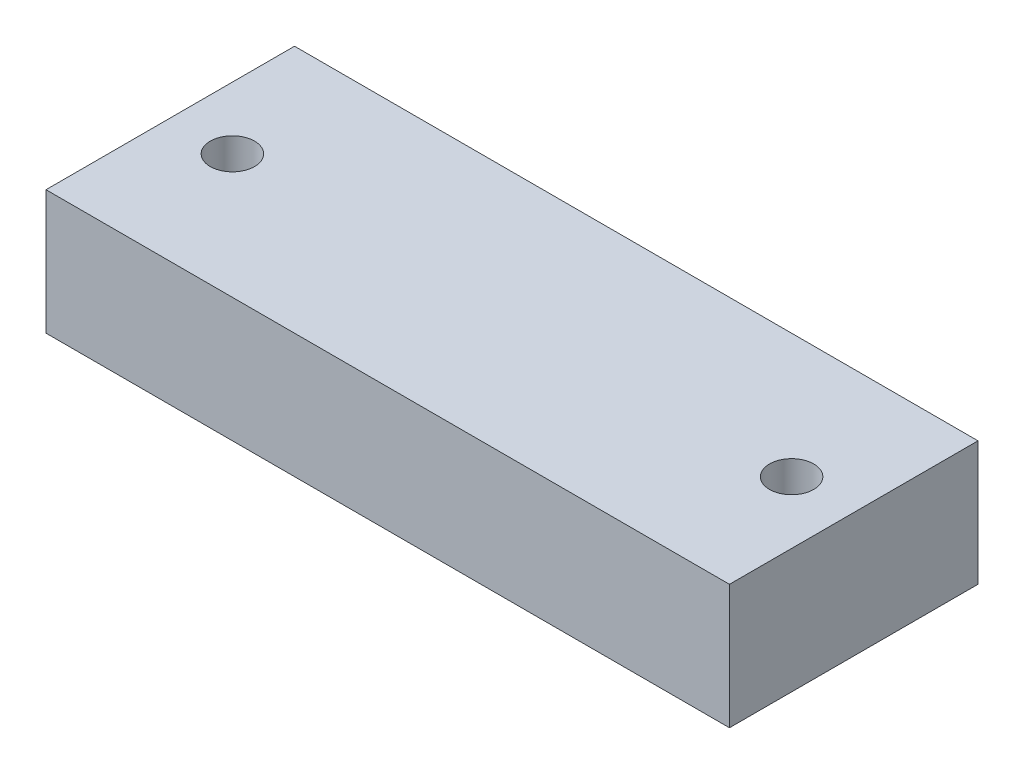
SolidWorks part; units mm, degrees
ref_plane "Front Plane" through (0, 0, 0) normal (0, 0, 1) x (1, 0, 0)
ref_plane "Top Plane" through (0, 0, 0) normal (0, 1, 0) x (1, 0, 0)
ref_plane "Right Plane" through (0, 0, 0) normal (1, 0, 0) x (0, 0, -1)
sketch "Sketch1" plane through (0, 0, 0) normal (0, 1, 0) x (1, 0, 0)
  line L1 (-17.4625, 6.35) -> (17.4625, 6.35)
  line L2 (-17.4625, 6.35) -> (-17.4625, -6.35)
  line L3 (-17.4625, -6.35) -> (17.4625, -6.35)
  line L4 (17.4625, 6.35) -> (17.4625, -6.35)
  line L5 (-17.4625, 6.35) -> (17.4625, -6.35) construction
  line L6 (-17.4625, -6.35) -> (17.4625, 6.35) construction
  point P0 (0, 0)
  dimension "D1" = 34.925
  dimension "D2" = 12.7
extrude "Boss-Extrude1" add sketch "Sketch1" along normal blind 6.35
hole_wizard "#4-40 Tapped Hole1" positions "Sketch2" profile "Sketch3" tap size "#4-40" standard "ANSI Inch" end condition through all
sketch "Sketch2" plane through (0, 6.35, 0) normal (0, 1, 0) x (1, 0, 0)
  line L0 (-17.4625, 6.35) -> (-17.4625, -6.35) construction
  line L1 (17.4625, -6.35) -> (17.4625, 6.35) construction
  point P0 (-14.2875, 0)
  point P3 (14.2875, 0)
  point P7 (0, 0)
  point P10 (0, 0)
  point P11 (-17.4625, 0)
  point P12 (0, 0)
  dimension "D1" = 3.175
  dimension "D2" = 3.175
sketch "Sketch3" plane through (-14.2875, 6.35, 0) normal (1, 0, 0) x (0, 0, 1)
  line L0 (0, 0) -> (0, 6.35)
  line L1 (0, 6.35) -> (1.1303, 6.35)
  line L2 (1.1303, 6.35) -> (1.1303, 0)
  line L5 (1.1303, 0) -> (0, 0)
  line L11 (0, -6.35) -> (0, 107.95) construction
  dimension "Thru Tap Drill Dia." = 2.2606
  dimension "Thru Tap Drill Depth" = 6.35
cosmetic thread "Hole Thread1" parameters "D2"=2.8448
cosmetic thread "Hole Thread2" parameters "D2"=2.8448
